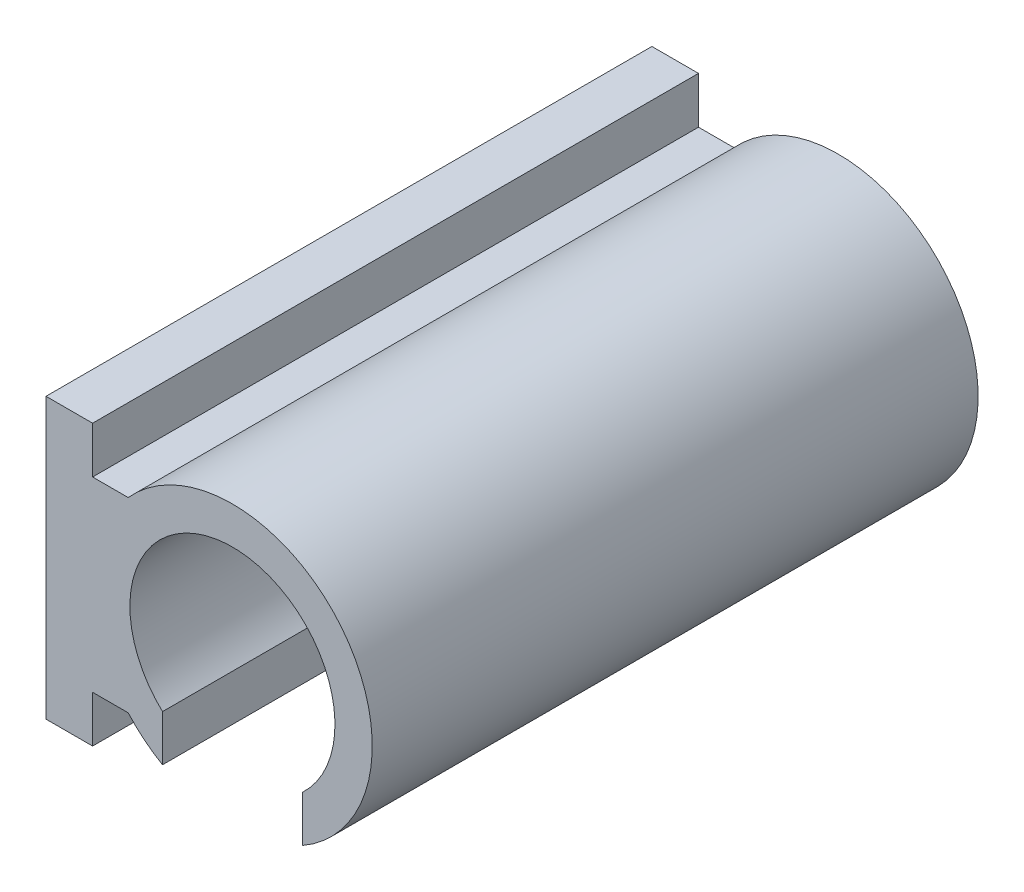
SolidWorks part; units mm, degrees
ref_plane "Front Plane" through (0, 0, 0) normal (0, 0, 1) x (1, 0, 0)
ref_plane "Top Plane" through (0, 0, 0) normal (0, 1, 0) x (1, 0, 0)
ref_plane "Right Plane" through (0, 0, 0) normal (1, 0, 0) x (0, 0, -1)
sketch "Sketch2" plane through (0, 0, 0) normal (0, 0, 1) x (1, 0, 0)
  circle A0 centre (0, 0) radius 30
  dimension "D1" = 60
extrude "Boss-Extrude2" add sketch "Sketch2" along normal blind 130
sketch "Sketch3" plane through (0, 0, 130) normal (0, 0, 1) x (1, 0, 0)
  circle A0 centre (0, 0) radius 22
  dimension "D1" = 44
extrude "Cut-Extrude1" cut sketch "Sketch3" against normal through all
ref_plane "Plane1" through (0, -30, 0) normal (0, 1, 0) x (1, 0, 0)
sketch "Sketch4" plane through (0, -30, 0) normal (0, 1, 0) x (1, 0, 0)
  line L1 (15, -140) -> (-15, -140)
  line L2 (15, -140) -> (15, 0)
  line L3 (15, 0) -> (-15, 0)
  line L4 (-15, -140) -> (-15, 0)
  dimension "D1" = 140
  dimension "D2" = 30
  dimension "D3" = 15
extrude "Cut-Extrude2" cut sketch "Sketch4" along normal up to next
ref_plane "Plane2" through (-30, 0, 0) normal (1, 0, 0) x (0, 0, -1)
sketch "Sketch5" plane through (-30, 0, 0) normal (1, 0, 0) x (0, 0, -1)
  line L1 (-130, -20) -> (0, -20)
  line L2 (-130, -20) -> (-130, 20)
  line L3 (-130, 20) -> (0, 20)
  line L4 (0, -20) -> (0, 20)
  dimension "D1" = 130
  dimension "D2" = 40
  dimension "D3" = 20
extrude "Boss-Extrude3" add sketch "Sketch5" along normal up to next
sketch "Sketch6" plane through (-30, 0, 0) normal (-1, 0, 0) x (0, 0, 1)
  line L0 (130, 20) -> (130, -20) construction
  line L5 (0, -30) -> (130, -30)
  line L6 (0, -30) -> (0, 30)
  line L7 (0, 30) -> (130, 30)
  line L8 (130, -30) -> (130, 30)
  line L9 (0, -20) -> (0, 20) construction
  point P10 (0, 0)
  dimension "D1" = 60
extrude "Boss-Extrude4" add sketch "Sketch6" along normal blind 10
